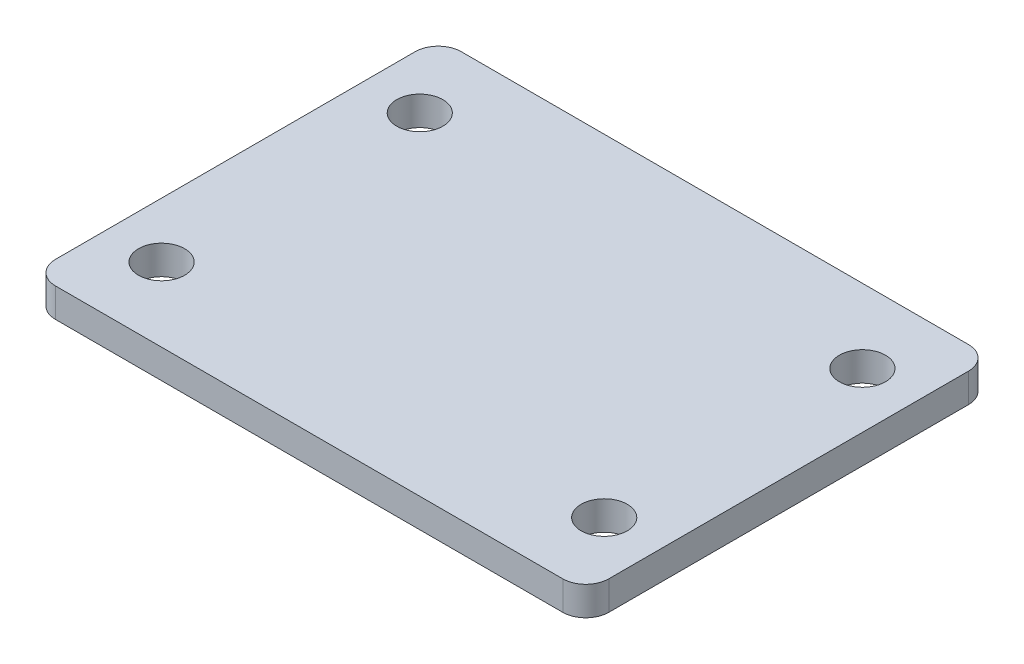
SolidWorks part; units mm, degrees
ref_plane "Front Plane" through (0, 0, 0) normal (0, 0, 1) x (1, 0, 0)
ref_plane "Top Plane" through (0, 0, 0) normal (0, 1, 0) x (1, 0, 0)
ref_plane "Right Plane" through (0, 0, 0) normal (1, 0, 0) x (0, 0, -1)
sketch "Sketch1" plane through (0, 0, 0) normal (0, 1, 0) x (1, 0, 0)
  line L0 (-47.625, 34.925) -> (47.625, -34.925) construction
  line L1 (-43.6626, 34.925) -> (43.6626, 34.925)
  line L2 (-47.625, 30.9626) -> (-47.625, -30.9626)
  line L3 (-43.6626, -34.925) -> (43.6626, -34.925)
  line L4 (47.625, 30.9626) -> (47.625, -30.9626)
  line L8 (0, 0) -> (0, 34.925) construction
  line L9 (0, 0) -> (47.625, 0) construction
  circle A0 centre (-38.1, 22.225) radius 3.9687
  circle A1 centre (-38.1, -22.225) radius 3.9687
  circle A2 centre (38.1, -22.225) radius 3.9687
  circle A3 centre (38.1, 22.225) radius 3.9687
  arc A4 (-47.625, -30.9626) -> (-43.6626, -34.925) centre (-43.6626, -30.9626) ccw
  arc A5 (43.6626, -34.925) -> (47.625, -30.9626) centre (43.6626, -30.9626) ccw
  arc A6 (43.6626, 34.925) -> (47.625, 30.9626) centre (43.6626, 30.9626) cw
  arc A7 (-43.6626, 34.925) -> (-47.625, 30.9626) centre (-43.6626, 30.9626) ccw
  point P24 (47.625, 34.925)
  dimension "D2" = 44.45
  dimension "D3" = 7.9375
  dimension "D4" = 3.9624
  dimension "D1" = 76.2
  dimension "Plate Width" = 69.85
extrude "Boss-Extrude1" add sketch "Sketch1" along normal blind 5
